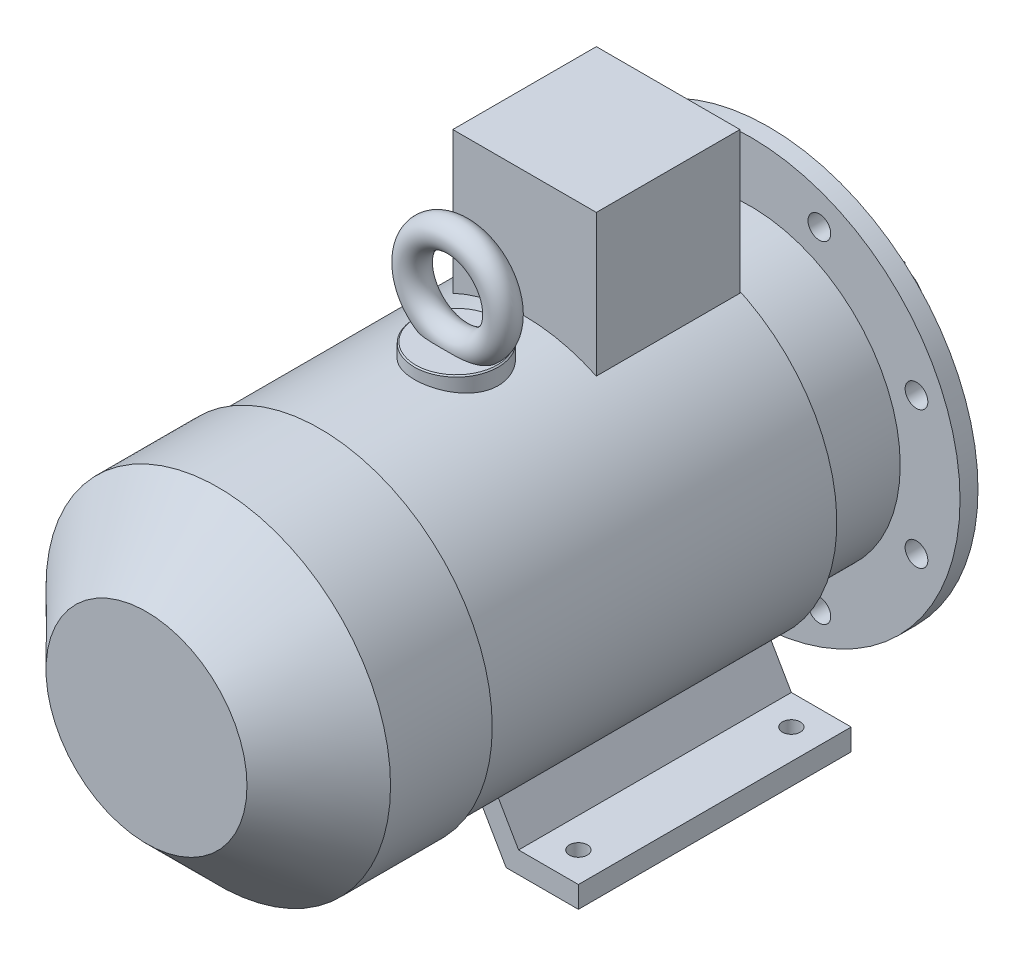
SolidWorks part; units mm, degrees
material "Ст.3 ГОСТ 380-88"
ref_plane "Спереди" through (0, 0, 0) normal (0, 0, 1) x (1, 0, 0)
ref_plane "Сверху" through (0, 0, 0) normal (0, 1, 0) x (1, 0, 0)
ref_plane "Справа" through (0, 0, 0) normal (1, 0, 0) x (0, 0, -1)
sketch "Эскиз1" plane through (0, 0, 0) normal (0, 0, 1) x (1, 0, 0)
  circle A0 centre (0, 0) radius 21
  dimension "D1" = 42
extrude "Вытянуть1" add sketch "Эскиз1" along normal blind 110
sketch "Эскиз2" plane through (0, 0, 0) normal (0, 0, -1) x (-1, 0, 0)
  line L0 (0, 0) -> (0, 24.6027) construction
  line L2 (-4, 24) -> (4, 24)
  line L3 (-4, 24) -> (-4, 16)
  line L4 (-4, 16) -> (4, 16)
  line L5 (4, 24) -> (4, 16)
  circle A1 centre (0, 0) radius 21 construction
  dimension "D1" = 8
  dimension "D2" = 8
  dimension "D3" = 45
extrude "Вытянуть2" add sketch "Эскиз2" against normal blind 55 and the other way blind 0.1
sketch "Эскиз3" plane through (0, 0, 110) normal (0, 0, 1) x (1, 0, 0)
  circle A0 centre (0, 0) radius 175
  dimension "D1" = 350
extrude "Вытянуть3" add sketch "Эскиз3" along normal blind 15
sketch "Эскиз4" plane through (0, 0, 110) normal (0, 0, -1) x (-1, 0, 0)
  circle A0 centre (0, 0) radius 125
  circle A1 centre (0, 0) radius 116
  dimension "D1" = 250
  dimension "D2" = 232
extrude "Вытянуть4" add sketch "Эскиз4" along normal blind 5
sketch "Эскиз5" plane through (0, 0, 110) normal (0, 0, -1) x (-1, 0, 0)
  circle A0 centre (0, 0) radius 116
  circle A1 centre (0, 0) radius 40
  dimension "D1" = 232
  dimension "D2" = 80
extrude "Вырез-Вытянуть1" cut sketch "Эскиз5" against normal blind 8
chamfer "Фаска1" distance 1 angle 45 3 edges at (-125, 0, 105) (-40, 0, 110) (0, -21, 0)
sketch "Эскиз6" plane through (0, 0, 110) normal (0, 0, -1) x (-1, 0, 0)
  line L0 (0, 0) -> (0, 218.5331) construction
  line L1 (0, 0) -> (-85.0868, 205.4176) construction
  circle A0 centre (-57.4025, 138.5819) radius 9.5
  circle A2 centre (57.4025, 138.5819) radius 9.5
  circle A3 centre (138.5819, 57.4025) radius 9.5
  circle A4 centre (138.5819, -57.4025) radius 9.5
  circle A5 centre (57.4025, -138.5819) radius 9.5
  circle A6 centre (-57.4025, -138.5819) radius 9.5
  circle A7 centre (-138.5819, -57.4025) radius 9.5
  circle A8 centre (-138.5819, 57.4025) radius 9.5
  dimension "D2" = 19
  dimension "D1" = 22.5
  dimension "D3" = 150
  dimension "D4" = 150
  dimension "D5" = 150
extrude "Вырез-Вытянуть2" cut sketch "Эскиз6" against normal through all
sketch "Эскиз7" plane through (0, 0, 125) normal (0, 0, 1) x (1, 0, 0)
  circle A0 centre (0, 0) radius 125
  dimension "D1" = 250
extrude "Вытянуть5" add sketch "Эскиз7" along normal blind 68
sketch "Эскиз8" plane through (0, 0, 193) normal (0, 0, 1) x (1, 0, 0)
  circle A0 centre (0, 0) radius 140
  dimension "D1" = 280
extrude "Вытянуть6" add sketch "Эскиз8" along normal blind 292
sketch "Эскиз9" plane through (0, 0, 485) normal (0, 0, 1) x (1, 0, 0)
  circle A0 centre (0, 0) radius 144
  dimension "D1" = 288
extrude "Вытянуть7" add sketch "Эскиз9" along normal blind 145
chamfer "Фаска2" distance 60 angle 45 1 edges at (144, 0, 630)
sketch "Эскиз10" plane through (0, 0, 193) normal (0, 0, -1) x (-1, 0, 0)
  line L0 (0, 0) -> (0, -216.5066) construction
  line L1 (-152, -160) -> (-91.6077, -160)
  line L2 (-91.6077, -160) -> (-51.9454, -91.303)
  line L3 (-51.9454, -91.303) -> (-67.5339, -82.303)
  line L4 (-67.5339, -82.303) -> (-102, -142)
  line L5 (-102, -142) -> (-152, -142)
  line L6 (-152, -142) -> (-152, -160)
  line L7 (91.6077, -160) -> (51.9454, -91.303)
  line L8 (152, -160) -> (91.6077, -160)
  line L9 (152, -142) -> (152, -160)
  line L10 (102, -142) -> (152, -142)
  line L11 (67.5339, -82.303) -> (102, -142)
  line L12 (51.9454, -91.303) -> (67.5339, -82.303)
  dimension "D1" = 18
  dimension "D2" = 18
  dimension "D3" = 30
  dimension "D4" = 50
  dimension "D5" = 152
  dimension "D6" = 160
  dimension "D7" = 105.0434
extrude "Вытянуть8" add sketch "Эскиз10" against normal blind 228
sketch "Эскиз11" plane through (0, -160, 0) normal (0, -1, 0) x (1, 0, 0)
  line L0 (-211.0007, 218) -> (224.3783, 218) construction
  line L1 (0, 0) -> (0, 657.2941) construction
  line L2 (-127, 218) -> (127, 218) construction
  line L3 (-127, 218) -> (-127, 396) construction
  circle A0 centre (-127, 218) radius 7.5
  circle A1 centre (127, 218) radius 7.5
  circle A2 centre (-127, 396) radius 7.5
  circle A3 centre (127, 396) radius 7.5
  dimension "D2" = 15
  dimension "D1" = 218
  dimension "D3" = 127
  dimension "D4" = 90
  dimension "D5" = 396
  dimension "D6" = 254
  dimension "D7" = 178
extrude "Вырез-Вытянуть3" cut sketch "Эскиз11" against normal up to next
sketch "Эскиз12" plane through (0, 0, 0) normal (0, 1, 0) x (1, 0, 0)
  line L0 (0, 0) -> (0, -277.4752) construction
  line L2 (-60, -194) -> (60, -194)
  line L3 (-60, -194) -> (-60, -314)
  line L4 (-60, -314) -> (60, -314)
  line L5 (60, -194) -> (60, -314)
  line L6 (140, -193) -> (-140, -193) construction
  dimension "D1" = 120
  dimension "D2" = 120
  dimension "D3" = 1
extrude "Вытянуть9" add sketch "Эскиз12" along normal blind 245
sketch "Эскиз13" plane through (0, 0, 0) normal (0, 1, 0) x (1, 0, 0)
  line L0 (0, -1) -> (0, -457.8467) construction
  line L1 (-21, -1) -> (21, -1) construction
  circle A0 centre (0, -371) radius 35
  dimension "D1" = 70
  dimension "D2" = 370
extrude "Вытянуть10" add sketch "Эскиз13" along normal blind 150
chamfer "Фаска3" distance 1 angle 45 1 edges at (0, 150, 406)
ref_plane "Плоскость1" through (0, 0, 370) normal (0, 0, 1) x (1, 0, 0)
sketch "Эскиз14" plane through (0, 0, 370) normal (0, 0, 1) x (1, 0, 0)
  line L0 (0, 0) -> (0, 273.5288) construction
  line L1 (34, 150) -> (-34, 150) construction
  circle A0 centre (0, 188) radius 38
  dimension "D1" = 76
sketch "Эскиз15" plane through (0, 0, 0) normal (1, 0, 0) x (0, 0, -1)
  line L0 (-370, 0) -> (-370, 273.5288) construction
  line L1 (-370, 226) -> (-370, 150) construction
  line L2 (-337, 150) -> (-405, 150) construction
  circle A0 centre (-370, 226) radius 12
  dimension "D1" = 24
  dimension "D2" = 76
sweep "По траектории1" add profiles "Эскиз15" path "Эскиз14"
sketch "Эскиз16" plane through (-60, 0, 0) normal (-1, 0, 0) x (0, 0, 1)
  line L0 (194, 245) -> (314, 245) construction
  line L1 (194, 245) -> (194, 126.4911) construction
  circle A0 centre (254, 185) radius 16
  dimension "D1" = 32
  dimension "D2" = 60
  dimension "D3" = 60
extrude "Вытянуть11" add sketch "Эскиз16" along normal blind 14
sketch "Эскиз17" plane through (-74, 0, 0) normal (-1, 0, 0) x (0, 0, 1)
  line L0 (254, 185) -> (254, 256.276) construction
  line L1 (254, 207.5167) -> (234.5, 196.2583)
  line L2 (234.5, 196.2583) -> (234.5, 173.7417)
  line L3 (234.5, 173.7417) -> (254, 162.4833)
  line L4 (254, 162.4833) -> (273.5, 173.7417)
  line L5 (273.5, 173.7417) -> (273.5, 196.2583)
  line L6 (273.5, 196.2583) -> (254, 207.5167)
  circle A0 centre (254, 185) radius 19.5 construction
  circle A1 centre (254, 185) radius 16 construction
  dimension "D1" = 39
extrude "Вытянуть12" add sketch "Эскиз17" along normal blind 16
sketch "Эскиз18" plane through (-90, 0, 0) normal (-1, 0, 0) x (0, 0, 1)
  circle A0 centre (254, 185) radius 7
  circle A1 centre (254, 185) radius 16 construction
  dimension "D1" = 14
extrude "Вырез-Вытянуть4" cut sketch "Эскиз18" against normal blind 16
